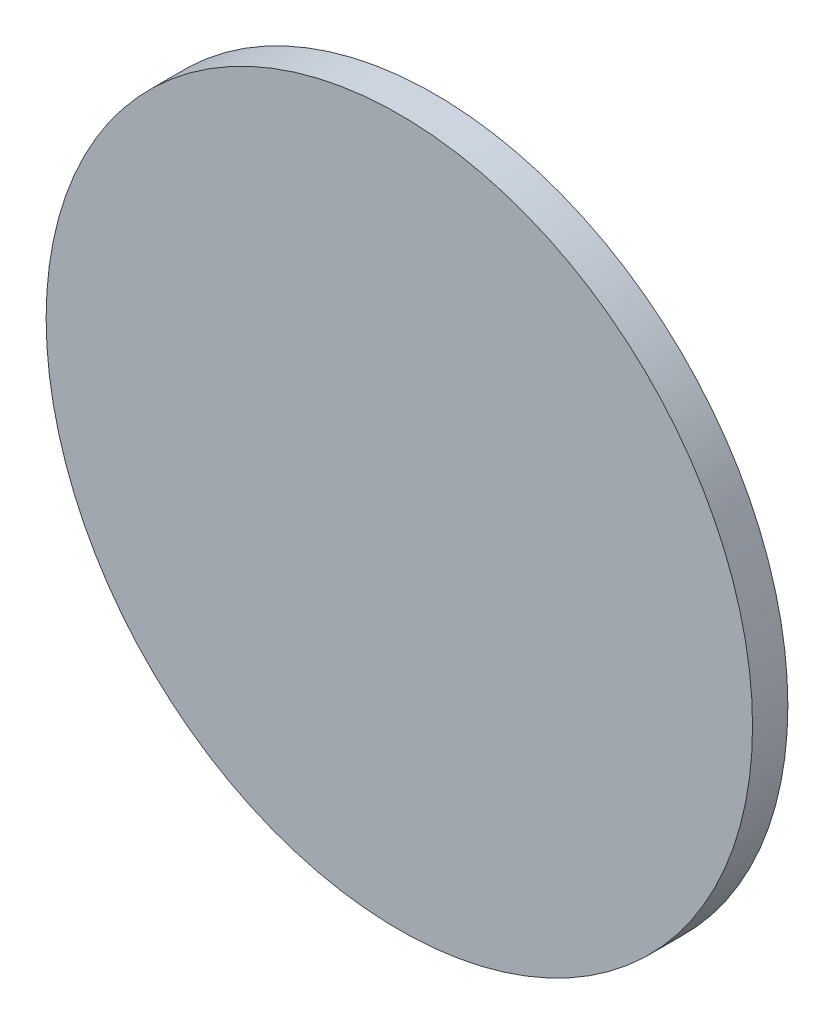
SolidWorks part; units mm, degrees
ref_plane "Front Plane" through (0, 0, 0) normal (0, 0, 1) x (1, 0, 0)
ref_plane "Top Plane" through (0, 0, 0) normal (0, 1, 0) x (1, 0, 0)
ref_plane "Right Plane" through (0, 0, 0) normal (1, 0, 0) x (0, 0, -1)
sketch "Sketch1" plane through (0, 0, 0) normal (0, 0, 1) x (1, 0, 0)
  circle A0 centre (0, 0) radius 200
extrude "Boss-Extrude1" add sketch "Sketch1" along normal blind 20
sketch "Sketch2" plane through (0, 0, 20) normal (0, 0, 1) x (1, 0, 0)
  circle A0 centre (0, 0) radius 180
ref_plane "Plane1" through (0, 0, 20) normal (0, 0, 1) x (1, 0, 0)
sketch "Sketch5" plane through (0, 0, 20) normal (0, 0, 1) x (1, 0, 0)
  line L0 (-25, -80) -> (25, -80)
  line L1 (25, -80) -> (25, 40)
  line L2 (-25, -80) -> (-25, 40)
  line L3 (-25, 40) -> (-55, 40)
  line L4 (25, 40) -> (55, 40)
  line L7 (-55, 40) -> (0, 110.2308)
  line L8 (0, 110.2308) -> (55, 40)
  point P2 (0, -80)
  dimension "D1" = 80
